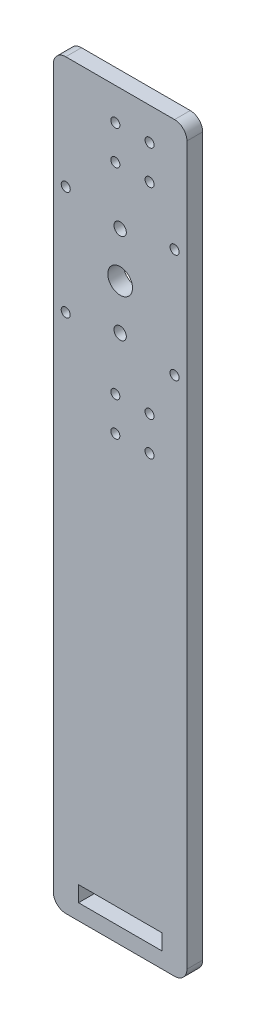
SolidWorks part; units mm, degrees
ref_plane "Front Plane" through (0, 0, 0) normal (0, 0, 1) x (1, 0, 0)
ref_plane "Top Plane" through (0, 0, 0) normal (0, 1, 0) x (1, 0, 0)
ref_plane "Right Plane" through (0, 0, 0) normal (1, 0, 0) x (0, 0, -1)
sketch "Sketch1" plane through (0, 0, 0) normal (0, 0, 1) x (1, 0, 0)
  line L0 (-27, -150) -> (-27, 150)
  line L1 (-27, -150) -> (27, -150)
  line L2 (-27, 150) -> (27, 150)
  line L3 (27, -150) -> (27, 150)
  line L4 (-27, -150) -> (27, 150) construction
  line L5 (-27, 150) -> (27, -150) construction
  point P1 (0, 0)
  dimension "D1" = 54
  dimension "D2" = 300
extrude "Boss-Extrude1" add sketch "Sketch1" along normal blind 6.35
fillet "Fillet1" radius 5 4 edges at (27, -150, 3.175) (-27, -150, 3.175) (27, 150, 3.175) (-27, 150, 3.175)
sketch "Sketch2" plane through (0, 0, 6.35) normal (0, 0, 1) x (1, 0, 0)
  line L0 (4.97, 130) -> (4.97, 35) construction
  line L1 (22, 150) -> (-22, 150) construction
  line L2 (-1.9448, 123.0852) -> (-1.9448, 136.9148) construction
  line L3 (-1.9448, 123.0852) -> (11.8848, 123.0852) construction
  line L4 (-1.9448, 136.9148) -> (11.8848, 136.9148) construction
  line L5 (11.8848, 123.0852) -> (11.8848, 136.9148) construction
  line L6 (-1.9448, 123.0852) -> (11.8848, 136.9148) construction
  line L7 (-1.9448, 136.9148) -> (11.8848, 123.0852) construction
  line L8 (-1.9448, 28.0852) -> (-1.9448, 41.9148) construction
  line L9 (-1.9448, 28.0852) -> (11.8848, 28.0852) construction
  line L10 (-1.9448, 41.9148) -> (11.8848, 41.9148) construction
  line L11 (11.8848, 28.0852) -> (11.8848, 41.9148) construction
  line L12 (-1.9448, 28.0852) -> (11.8848, 41.9148) construction
  line L13 (-1.9448, 41.9148) -> (11.8848, 28.0852) construction
  line L14 (-22, 60.5) -> (-22, 104.5) construction
  line L15 (-22, 60.5) -> (22, 60.5) construction
  line L16 (-22, 104.5) -> (22, 104.5) construction
  line L17 (22, 60.5) -> (22, 104.5) construction
  line L18 (-22, 60.5) -> (22, 104.5) construction
  line L19 (-22, 104.5) -> (22, 60.5) construction
  line L20 (0, 64.25) -> (0, 100.75) construction
  point P2 (4.97, 82.5)
  point P3 (0, 82.5)
  point P7 (0, 82.5)
  point P22 (0, 82.5)
  dimension "D1" = 95
  dimension "D2" = 20
  dimension "D3" = 19.558
  dimension "D4" = 44
  dimension "D5" = 36.5
  dimension "D6" = 4.97
sketch "Sketch3" plane through (0, 0, 6.35) normal (0, 0, 1) x (1, 0, 0)
  circle A0 centre (0, 82.5) radius 5
  dimension "D1" = 10
extrude "Cut-Extrude1" cut sketch "Sketch3" against normal through all
hole_wizard "#6 Clearance Hole1" positions "Sketch5" profile "Sketch4" hole size "#6" standard "ANSI Inch" end condition through all
sketch "Sketch5" plane through (0, 0, 6.35) normal (0, 0, 1) x (1, 0, 0)
  point P0 (-22, 104.5)
  point P3 (-22, 60.5)
  point P6 (22, 60.5)
  point P9 (22, 104.5)
  point P12 (-1.9448, 123.0852)
  point P15 (-1.9448, 136.9148)
  point P18 (11.8848, 136.9148)
  point P21 (11.8848, 123.0852)
  point P24 (-1.9448, 41.9148)
  point P27 (11.8848, 41.9148)
  point P30 (11.8848, 28.0852)
  point P33 (-1.9448, 28.0852)
sketch "Sketch4" plane through (-22, 104.5, 6.35) normal (1, 0, 0) x (0, -1, 0)
  line L0 (0, 0) -> (0, 6.35)
  line L1 (0, 6.35) -> (1.8288, 6.35)
  line L2 (1.8288, 6.35) -> (1.8288, 0)
  line L5 (1.8288, 0) -> (0, 0)
  line L11 (0, -6.35) -> (0, 107.95) construction
  dimension "Thru Hole Dia." = 3.6576
  dimension "Thru Hole Depth" = 6.35
sketch "Sketch6" plane through (0, 0, 6.35) normal (0, 0, 1) x (1, 0, 0)
  line L0 (-16.825, -137.3) -> (-16.825, -143.65)
  line L1 (-16.825, -137.3) -> (16.825, -137.3)
  line L2 (-16.825, -143.65) -> (16.825, -143.65)
  line L3 (16.825, -137.3) -> (16.825, -143.65)
  line L4 (-16.825, -137.3) -> (16.825, -143.65) construction
  line L5 (-16.825, -143.65) -> (16.825, -137.3) construction
  line L6 (-22, -150) -> (22, -150) construction
  point P1 (0, -140.475)
  dimension "D1" = 6.35
  dimension "D2" = 33.65
  dimension "D3" = 6.35
extrude "Cut-Extrude2" cut sketch "Sketch6" against normal through all
hole_wizard "#10 Clearance Hole2" positions "Sketch10" profile "Sketch9" hole size "#10" standard "ANSI Inch" end condition through all
sketch "Sketch10" plane through (0, 0, 6.35) normal (0, 0, 1) x (1, 0, 0)
  point P0 (0, 64.25)
  point P3 (0, 100.75)
sketch "Sketch9" plane through (0, 64.25, 6.35) normal (1, 0, 0) x (0, -1, 0)
  line L0 (0, 0) -> (0, 6.35)
  line L1 (0, 6.35) -> (2.4892, 6.35)
  line L2 (2.4892, 6.35) -> (2.4892, 0)
  line L5 (2.4892, 0) -> (0, 0)
  line L11 (0, -6.35) -> (0, 107.95) construction
  dimension "Thru Hole Dia." = 4.9784
  dimension "Thru Hole Depth" = 6.35
